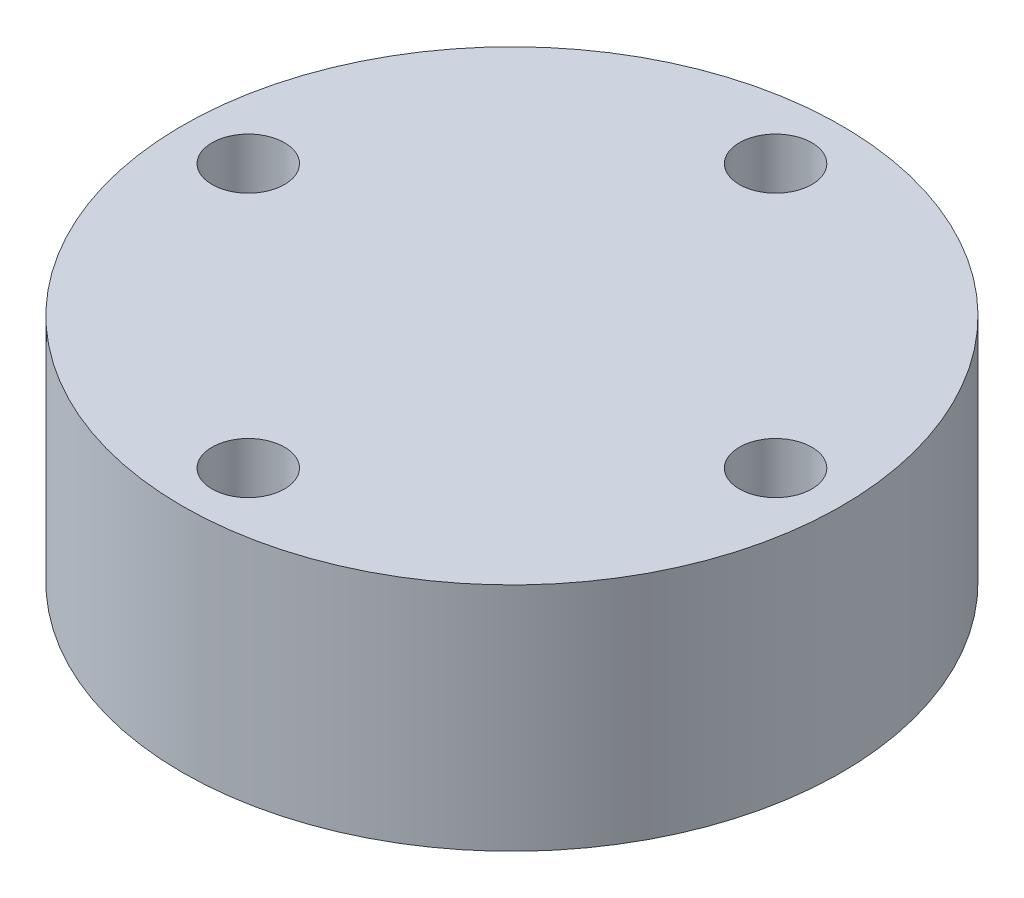
SolidWorks part; units mm, degrees
material "PVC 0.007 Plasticized"
ref_plane "Front Plane" through (0, 0, 0) normal (0, 0, 1) x (1, 0, 0)
ref_plane "Top Plane" through (0, 0, 0) normal (0, 1, 0) x (1, 0, 0)
ref_plane "Right Plane" through (0, 0, 0) normal (1, 0, 0) x (0, 0, -1)
sketch "Sketch1" plane through (0, 0, 0) normal (0, 1, 0) x (1, 0, 0)
  circle A0 centre (0, 0) radius 10
  circle A1 centre (0, 0) radius 8 construction
  circle A2 centre (0, 8) radius 1.1
  circle A3 centre (8, 0) radius 1.1
  circle A4 centre (0, -8) radius 1.1
  circle A5 centre (-8, 0) radius 1.1
  point P11 (0, 0)
  dimension "D1" = 20
  dimension "D2" = 16
  dimension "D3" = 2.2
extrude "Boss-Extrude1" add sketch "Sketch1" along normal blind 7
